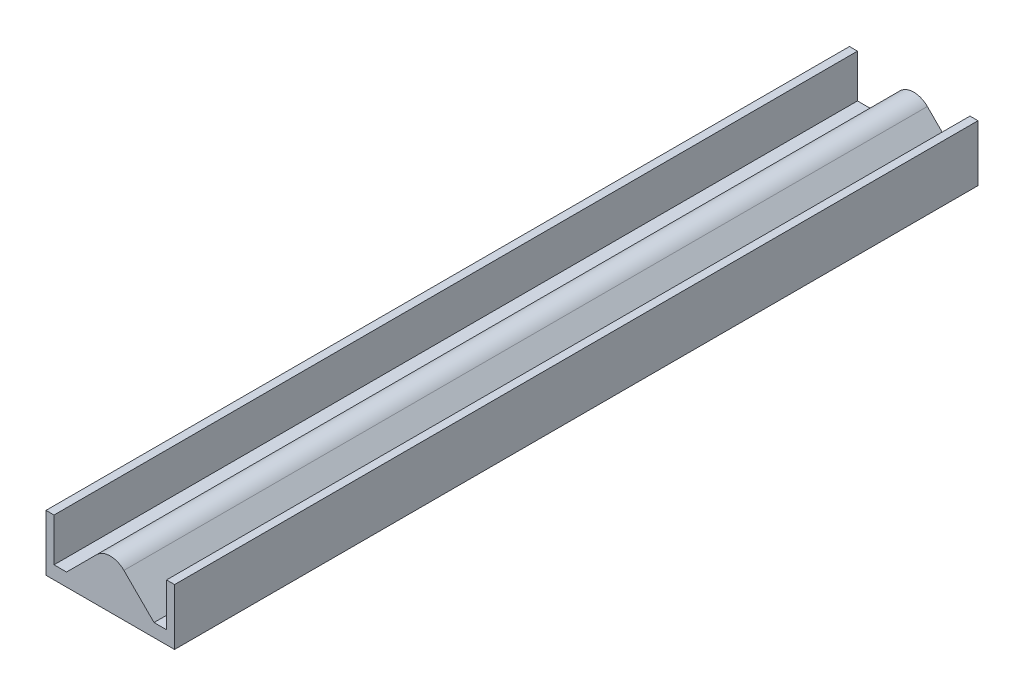
SolidWorks part; units mm, degrees
ref_plane "Front Plane" through (0, 0, 0) normal (0, 0, 1) x (1, 0, 0)
ref_plane "Top Plane" through (0, 0, 0) normal (0, 1, 0) x (1, 0, 0)
ref_plane "Right Plane" through (0, 0, 0) normal (1, 0, 0) x (0, 0, -1)
sketch "Sketch1" plane through (0, 0, 0) normal (0, 0, 1) x (1, 0, 0)
  line L0 (-40, 16.25) -> (-40, -18.75)
  line L1 (40, 16.25) -> (40, -18.75)
  line L2 (-40, 16.25) -> (40, -18.75) construction
  line L3 (-40, -18.75) -> (40, 16.25) construction
  line L4 (0, 18.75) -> (28.2843, -9.5343) construction
  line L5 (0, 18.75) -> (-28.2843, -9.5343) construction
  line L6 (0, 16.6287) -> (-27.2236, -10.5949)
  line L7 (0, 16.6287) -> (27.2236, -10.5949)
  line L8 (35, 16.25) -> (40, 16.25)
  line L9 (-35, 16.25) -> (-40, 16.25)
  line L10 (40, -18.75) -> (-40, -18.75)
  line L11 (-35, 16.25) -> (-35, -10.5949)
  line L12 (-35, -10.5949) -> (-27.2236, -10.5949)
  line L13 (35, 16.25) -> (35, -10.5949)
  line L14 (35, -10.5949) -> (27.2236, -10.5949)
  point P0 (0, -1.25)
  point P6 (0, -1.25)
  dimension "D1" = 80
  dimension "D2" = 35
  dimension "D3" = 45
  dimension "D4" = 45
  dimension "D5" = 40
  dimension "D6" = 40
  dimension "D7" = 5
  dimension "D8" = 5
extrude "Boss-Extrude1" add sketch "Sketch1" along normal blind 500
fillet "Fillet1" radius 12 1 edges at (0, 16.6287, 250)
